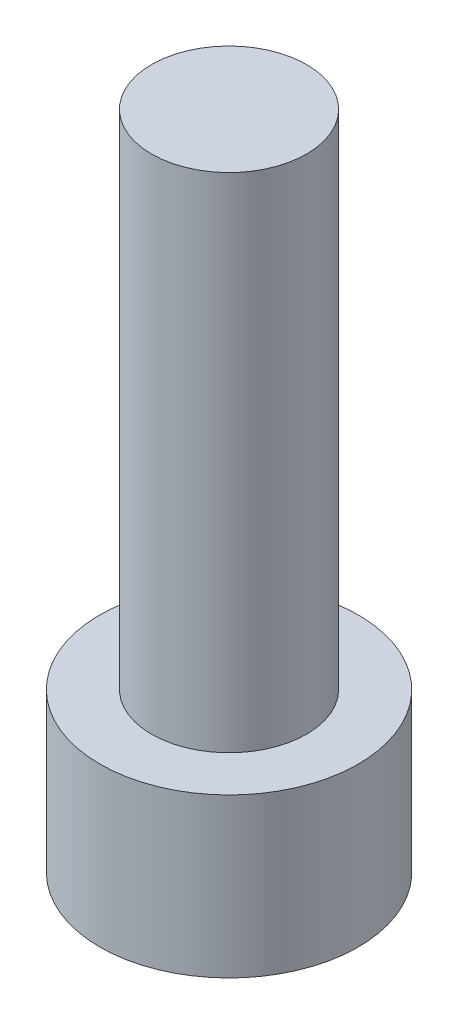
SolidWorks part; units mm, degrees
material "Plain Carbon Steel"
ref_plane "Front Plane" through (0, 0, 0) normal (0, 0, 1) x (1, 0, 0)
ref_plane "Top Plane" through (0, 0, 0) normal (0, 1, 0) x (1, 0, 0)
ref_plane "Right Plane" through (0, 0, 0) normal (1, 0, 0) x (0, 0, -1)
sketch "Sketch1" plane through (0, 0, 0) normal (0, 1, 0) x (1, 0, 0)
  circle A0 centre (0, 0) radius 2.8575
  dimension "D1" = 5.715
extrude "Boss-Extrude1" add sketch "Sketch1" along normal blind 3.5052
sketch "Sketch2" plane through (0, 0, 0) normal (0, -1, 0) x (1, 0, 0)
  line L1 (1.604, 0) -> (0.802, 1.3891)
  line L2 (0.802, 1.3891) -> (-0.802, 1.3891)
  line L3 (-0.802, 1.3891) -> (-1.604, 0)
  line L4 (-1.604, 0) -> (-0.802, -1.3891)
  line L5 (-0.802, -1.3891) -> (0.802, -1.3891)
  line L6 (0.802, -1.3891) -> (1.604, 0)
  circle A0 centre (0, 0) radius 1.3891 construction
  dimension "D1" = 2.7781
extrude "Cut-Extrude1" cut sketch "Sketch2" against normal blind 1.9558
sketch "Sketch3" plane through (0, 3.5052, 0) normal (0, 1, 0) x (1, 0, 0)
  circle A0 centre (0, 0) radius 1.7145
  dimension "D1" = 3.429
extrude "Boss-Extrude2" add sketch "Sketch3" along normal blind 11.1125
